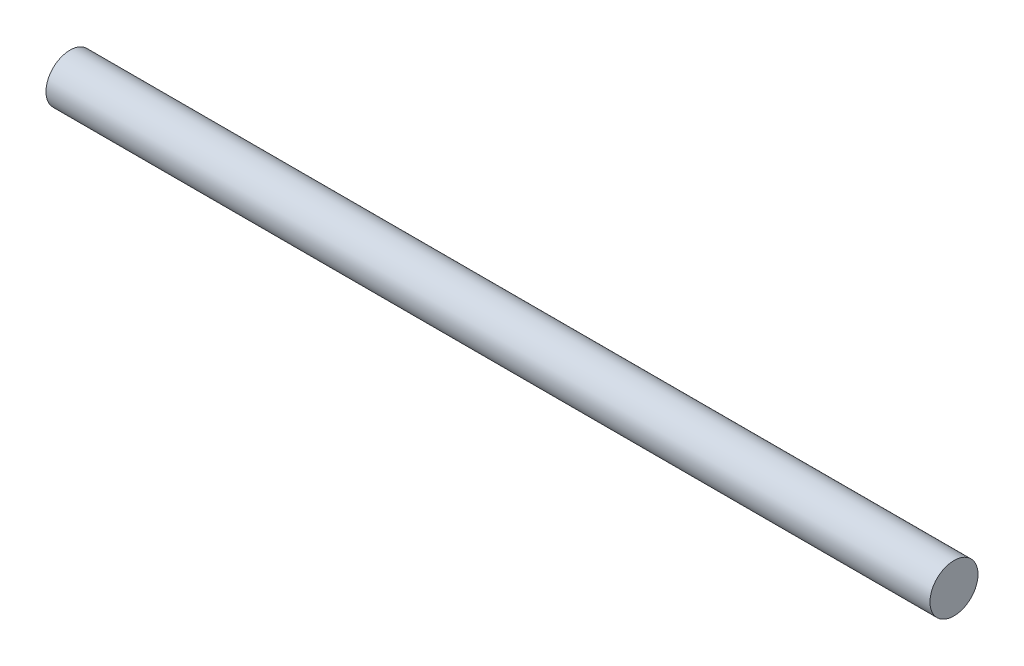
SolidWorks part; units mm, degrees
ref_plane "Front Plane" through (0, 0, 0) normal (0, 0, 1) x (1, 0, 0)
ref_plane "Top Plane" through (0, 0, 0) normal (0, 1, 0) x (1, 0, 0)
ref_plane "Right Plane" through (0, 0, 0) normal (1, 0, 0) x (0, 0, -1)
sketch "Sketch1" plane through (0, 0, 0) normal (1, 0, 0) x (0, 0, -1)
  circle A0 centre (0, 0) radius 6.35
  dimension "D1" = 12.7
extrude "Boss-Extrude1" add sketch "Sketch1" along normal blind 233.68
